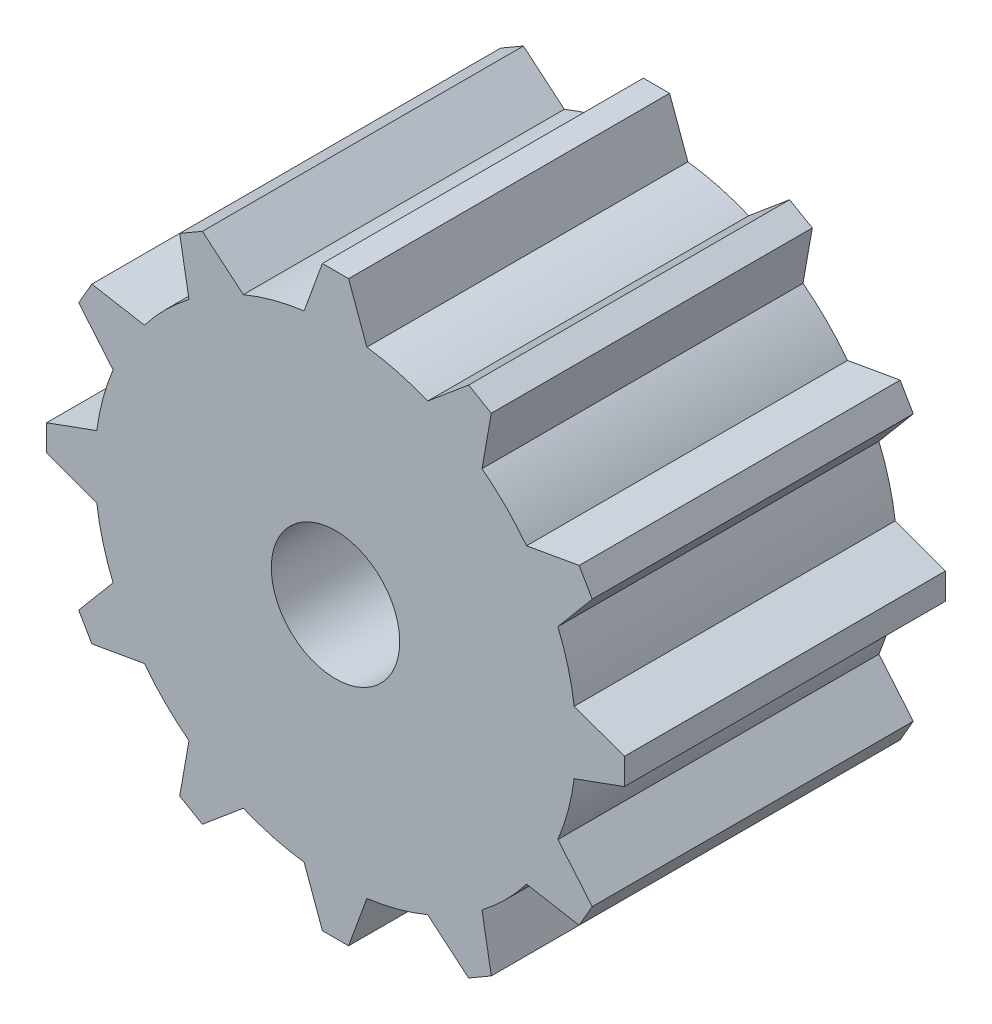
SolidWorks part; units mm, degrees
ref_plane "Ön Düzlem" through (0, 0, 0) normal (0, 0, 1) x (1, 0, 0)
ref_plane "Üst Düzlem" through (0, 0, 0) normal (0, 1, 0) x (1, 0, 0)
ref_plane "Sağ Düzlem" through (0, 0, 0) normal (1, 0, 0) x (0, 0, -1)
sketch "Çizim1" plane through (0, 0, 0) normal (0, 0, 1) x (1, 0, 0)
  circle A0 centre (0, 0) radius 7.5
  dimension "D1" = 15
extrude "Yükseklik-Ekstrüzyon1" add sketch "Çizim1" along normal mid plane 10
sketch "Çizim2" plane through (0, 0, 0) normal (0, 0, 1) x (1, 0, 0)
  line L0 (0, 0) -> (0, 7.5) construction
  line L1 (-1.5, 6) -> (1.5, 6)
  line L2 (1.5, 6) -> (0.4081, 9)
  line L3 (0.4081, 9) -> (-0.4081, 9)
  line L4 (-0.4081, 9) -> (-1.5, 6)
  line L5 (4.1466, 7.9983) -> (1.701, 5.9462)
  line L6 (1.701, 5.9462) -> (4.299, 4.4462)
  line L7 (4.299, 4.4462) -> (4.8534, 7.5902)
  line L8 (4.8534, 7.5902) -> (4.1466, 7.9983)
  line L9 (7.5902, 4.8534) -> (4.4462, 4.299)
  line L10 (4.4462, 4.299) -> (5.9462, 1.701)
  line L11 (5.9462, 1.701) -> (7.9983, 4.1466)
  line L12 (7.9983, 4.1466) -> (7.5902, 4.8534)
  line L13 (9, 0.4081) -> (6, 1.5)
  line L14 (6, 1.5) -> (6, -1.5)
  line L15 (6, -1.5) -> (9, -0.4081)
  line L16 (9, -0.4081) -> (9, 0.4081)
  line L17 (7.9983, -4.1466) -> (5.9462, -1.701)
  line L18 (5.9462, -1.701) -> (4.4462, -4.299)
  line L19 (4.4462, -4.299) -> (7.5902, -4.8534)
  line L20 (7.5902, -4.8534) -> (7.9983, -4.1466)
  line L21 (4.8534, -7.5902) -> (4.299, -4.4462)
  line L22 (4.299, -4.4462) -> (1.701, -5.9462)
  line L23 (1.701, -5.9462) -> (4.1466, -7.9983)
  line L24 (4.1466, -7.9983) -> (4.8534, -7.5902)
  line L25 (0.4081, -9) -> (1.5, -6)
  line L26 (1.5, -6) -> (-1.5, -6)
  line L27 (-1.5, -6) -> (-0.4081, -9)
  line L28 (-0.4081, -9) -> (0.4081, -9)
  line L29 (-4.1466, -7.9983) -> (-1.701, -5.9462)
  line L30 (-1.701, -5.9462) -> (-4.299, -4.4462)
  line L31 (-4.299, -4.4462) -> (-4.8534, -7.5902)
  line L32 (-4.8534, -7.5902) -> (-4.1466, -7.9983)
  line L33 (-7.5902, -4.8534) -> (-4.4462, -4.299)
  line L34 (-4.4462, -4.299) -> (-5.9462, -1.701)
  line L35 (-5.9462, -1.701) -> (-7.9983, -4.1466)
  line L36 (-7.9983, -4.1466) -> (-7.5902, -4.8534)
  line L37 (-9, -0.4081) -> (-6, -1.5)
  line L38 (-6, -1.5) -> (-6, 1.5)
  line L39 (-6, 1.5) -> (-9, 0.4081)
  line L40 (-9, 0.4081) -> (-9, -0.4081)
  line L41 (-7.9983, 4.1466) -> (-5.9462, 1.701)
  line L42 (-5.9462, 1.701) -> (-4.4462, 4.299)
  line L43 (-4.4462, 4.299) -> (-7.5902, 4.8534)
  line L44 (-7.5902, 4.8534) -> (-7.9983, 4.1466)
  line L45 (-4.8534, 7.5902) -> (-4.299, 4.4462)
  line L46 (-4.299, 4.4462) -> (-1.701, 5.9462)
  line L47 (-1.701, 5.9462) -> (-4.1466, 7.9983)
  line L48 (-4.1466, 7.9983) -> (-4.8534, 7.5902)
  circle A0 centre (0, 0) radius 7.5 construction
  point P56 (0, 0)
  dimension "D7" = 12
  dimension "D1" = 1.5
  dimension "D2" = 1.5
  dimension "D3" = 70
  dimension "D4" = 70
  dimension "D5" = 6
  dimension "D6" = 3
  dimension "D8" = 6
  dimension "D9" = 6
extrude "Yükseklik-Ekstrüzyon2" add sketch "Çizim2" along normal mid plane 10
sketch "Çizim3" plane through (0, 0, 5) normal (0, 0, 1) x (1, 0, 0)
  circle A0 centre (0, 0) radius 2
  dimension "D1" = 4
extrude "Kes-Ekstrüzyon1" cut sketch "Çizim3" against normal through all
